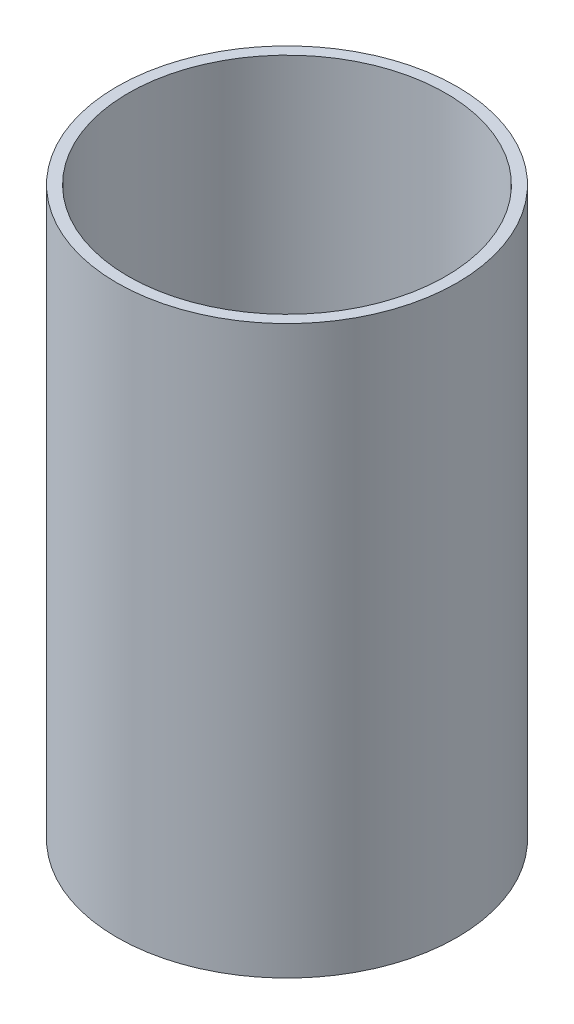
SolidWorks part; units mm, degrees
ref_plane "Front Plane" through (0, 0, 0) normal (0, 0, 1) x (1, 0, 0)
ref_plane "Top Plane" through (0, 0, 0) normal (0, 1, 0) x (1, 0, 0)
ref_plane "Right Plane" through (0, 0, 0) normal (1, 0, 0) x (0, 0, -1)
sketch "Sketch1" plane through (0, 0, 0) normal (0, 1, 0) x (1, 0, 0)
  circle A0 centre (0, 0) radius 30
  dimension "D1" = 60
extrude "Boss-Extrude1" add sketch "Sketch1" along normal blind 100
shell "Shell1" thickness 2
